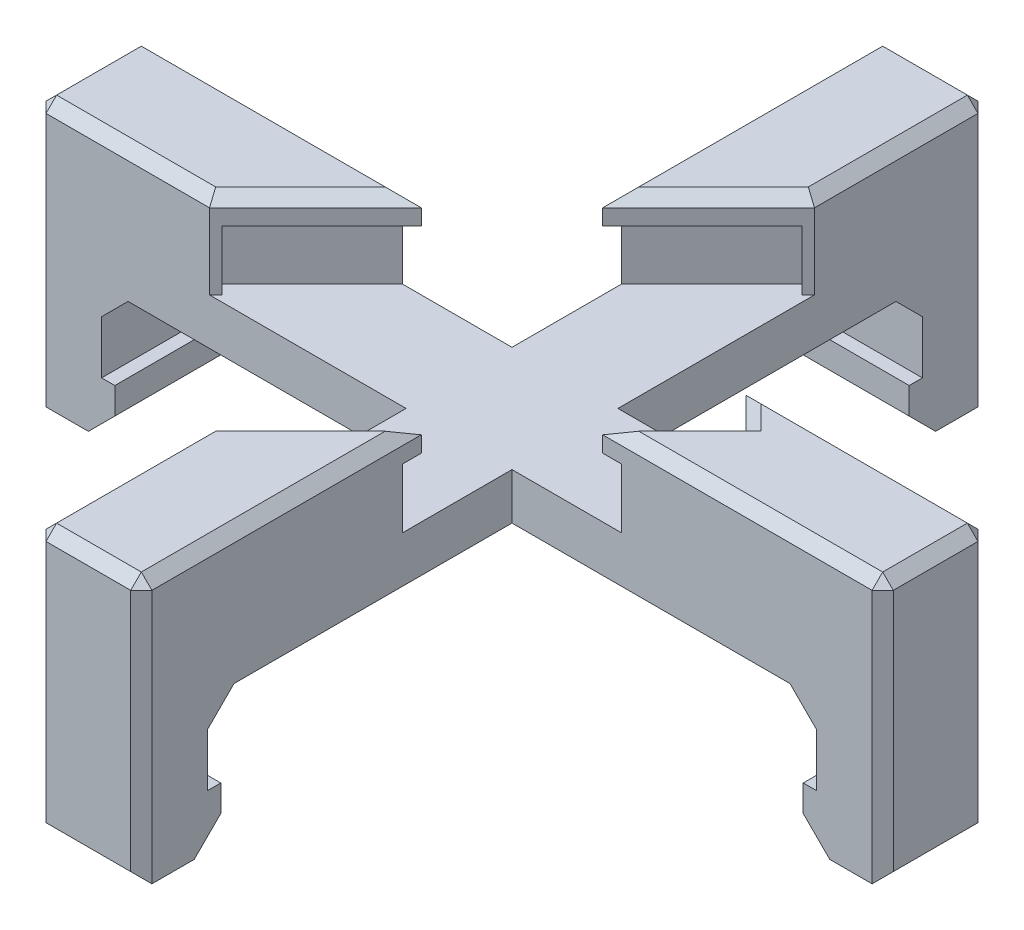
SolidWorks part; units mm, degrees
material "ABS"
ref_plane "Front Plane" through (0, 0, 0) normal (0, 0, 1) x (1, 0, 0)
ref_plane "Top Plane" through (0, 0, 0) normal (0, 1, 0) x (1, 0, 0)
ref_plane "Right Plane" through (0, 0, 0) normal (1, 0, 0) x (0, 0, -1)
sketch "Sketch1" plane through (0, 0, 0) normal (0, 1, 0) x (1, 0, 0)
  line L1 (16, -2) -> (-16, -2)
  line L2 (16, -2) -> (16, 2)
  line L3 (16, 2) -> (-16, 2)
  line L4 (-16, -2) -> (-16, 2)
  line L5 (16, -2) -> (-16, 2) construction
  line L6 (16, 2) -> (-16, -2) construction
  point P0 (0, 0)
  dimension "D1" = 32
  dimension "D2" = 4
extrude "Boss-Extrude1" add sketch "Sketch1" along normal blind 5
sketch "Sketch2" plane through (0, 0, 0) normal (0, -1, 0) x (1, 0, 0)
  line L0 (-13.5, 2) -> (13.5, -2) construction
  line L1 (16, -2) -> (-16, -2) construction
  line L2 (-16, 2) -> (16, 2) construction
  line L3 (13.5, -2) -> (16, -2)
  line L4 (13.5, -2) -> (13.5, 2)
  line L5 (13.5, 2) -> (16, 2)
  line L6 (16, -2) -> (16, 2)
  line L7 (16, 2) -> (16, -2) construction
  line L9 (-13.5, 2) -> (-16, 2)
  line L10 (-13.5, 2) -> (-13.5, -2)
  line L11 (-13.5, -2) -> (-16, -2)
  line L12 (-16, 2) -> (-16, -2)
  point P6 (0, 0)
  dimension "D1" = 27
extrude "Boss-Extrude2" add sketch "Sketch2" along normal blind 3
sketch "Sketch3" plane through (0, -3, 0) normal (0, -1, 0) x (1, 0, 0)
  line L0 (-13.5, 2) -> (13.5, 2) construction
  line L1 (16, -2) -> (13, -2)
  line L2 (16, -2) -> (16, 2)
  line L3 (16, 2) -> (13, 2)
  line L4 (13, -2) -> (13, 2)
  line L5 (13.5, 2) -> (13.5, -2) construction
  line L6 (13.5, -2) -> (-13.5, -2) construction
  line L7 (-16, 2) -> (-13, 2)
  line L8 (-16, 2) -> (-16, -2)
  line L9 (-16, -2) -> (-13, -2)
  line L10 (-13, 2) -> (-13, -2)
  line L11 (13.5, -2) -> (13, 2) construction
  line L12 (-13, 2) -> (-13.5, -2) construction
  dimension "D1" = 0.5
extrude "Boss-Extrude3" add sketch "Sketch3" along normal blind 2
sketch "Sketch5" plane through (0, 0, 0) normal (0, 0, 1) x (1, 0, 0)
  line L0 (0, 0) -> (0, -5) construction
pattern_circular "CirPattern1" count 2 every 90 about axis through (0, 0, 0) along (0, 1, 0) of "Boss-Extrude1", "Boss-Extrude3", "Boss-Extrude2"
sketch "Sketch6" plane through (0, 5, 0) normal (0, 1, 0) x (1, 0, 0)
  line L0 (-1.4142, -9.5459) -> (-9.5459, -1.4142)
  line L1 (-9.5459, -1.4142) -> (1.4142, 9.5459)
  line L2 (1.4142, 9.5459) -> (6.0104, 4.9497)
  line L3 (6.0104, 4.9497) -> (4.9497, 3.8891)
  line L4 (4.9497, 3.8891) -> (8.4853, 0.3536)
  line L5 (8.4853, 0.3536) -> (-1.4142, -9.5459)
  line L6 (-2, -2) -> (-2, -16) construction
  line L7 (-1.4142, -9.5459) -> (1.4142, 9.5459) construction
  point P3 (0, 0)
  dimension "D1" = 45
  dimension "D2" = 11.5
  dimension "D3" = 15.5
  dimension "D4" = 6.5
  dimension "D5" = 14
extrude "Cut-Extrude1" cut sketch "Sketch6" against normal blind 3.25
sketch "Sketch7" plane through (0, 5, 0) normal (0, 1, 0) x (1, 0, 0)
  line L0 (-9.5459, -1.4142) -> (-9.1924, -1.7678)
  line L4 (-9.1924, -1.7678) -> (-5.4246, 2)
  line L6 (-5.4246, 2) -> (-6.1317, 2)
  line L7 (-6.1317, 2) -> (-9.5459, -1.4142)
  line L8 (1.7678, 9.1924) -> (1.4142, 9.5459)
  line L9 (1.4142, 9.5459) -> (-2, 6.1317)
  line L10 (-2, 6.1317) -> (-2, 5.4246)
  line L11 (-2, 2) -> (-2, 6.1317) construction
  line L12 (-2, 5.4246) -> (1.7678, 9.1924)
  line L16 (8.1317, 0.7071) -> (8.4853, 0.3536)
  line L18 (8.4853, 0.3536) -> (6.8388, 2) construction
  line L19 (8.4853, 0.3536) -> (6.1317, -2)
  line L20 (6.1317, -2) -> (5.4246, -2)
  line L21 (6.1317, -2) -> (2, -2) construction
  line L22 (5.4246, -2) -> (8.1317, 0.7071)
  line L26 (2, -5.4246) -> (2, -6.1317)
  line L27 (2, -2) -> (2, -6.1317) construction
  line L28 (2, -6.1317) -> (-1.4142, -9.5459)
  line L29 (-1.4142, -9.5459) -> (-1.7678, -9.1924)
  line L31 (-2, -8.9602) -> (-1.4142, -9.5459) construction
  line L35 (-1.7678, -9.1924) -> (2, -5.4246)
  dimension "D2" = 0.5
extrude "Boss-Extrude4" add sketch "Sketch7" against normal blind 1
sketch "Sketch8" plane through (0, 5, 0) normal (0, 1, 0) x (1, 0, 0)
  line L0 (-9.4246, -2) -> (2, 9.4246)
  line L1 (-2, 5.4246) -> (1.7678, 9.1924) construction
  line L2 (-16, -2) -> (-8.9602, -2) construction
  line L3 (2, 8.9602) -> (2, 16) construction
extrude "Cut-Extrude-Thin1" cut sketch "Sketch8" against normal up to surface and the other way through all thin
sketch "Sketch9" plane through (0, 5, 0) normal (0, 1, 0) x (1, 0, 0)
  line L0 (2, -5.4246) -> (-2, -9.4246)
  line L1 (-2, -8.9602) -> (-2, -16) construction
  line L2 (2, -5.4246) -> (-1.7678, -9.1924) construction
extrude "Cut-Extrude-Thin2" cut sketch "Sketch9" against normal up to surface and the other way through all thin
chamfer "Chamfer2" distance 1 angle 45 8 edges at (0, 0, 13.5) (0, -5, -13) (0, -5, 13) (13.5, 0, 0) (-13.5, 0, 0) (13, -5, 0) (-13, -5, 0) (0, 0, -13.5)
chamfer "Chamfer3" distance 0.4 angle 45 29 edges at (16, 5, 0) (0, -5, -16) (0, -5, 16) (11.4194, 5, -2) (10.7123, 5, 2) (-10.7123, 5, -2) (-7.4246, 5, 0) (0, 5, -7.4246) (7.4853, 5, -1.3536) (6.7782, 5, 0.6464) (0, 5, 7.4246) (2, 5, -12.7123) (-2, 5, 12.7123) (16, -5, 0) (-16, 5, 0) (-16, -5, 0) (-12.7123, 5, 2) (0, 5, 16) (2, 5, 10.7123) (0, 5, -16) (-2, 5, -10.7123) (2, 0, 16) (-2, 0, -16) (-16, 0, -2) (-2, 0, 16) (2, 0, -16) (16, 0, -2) (16, 0, 2) (-16, 0, 2)
